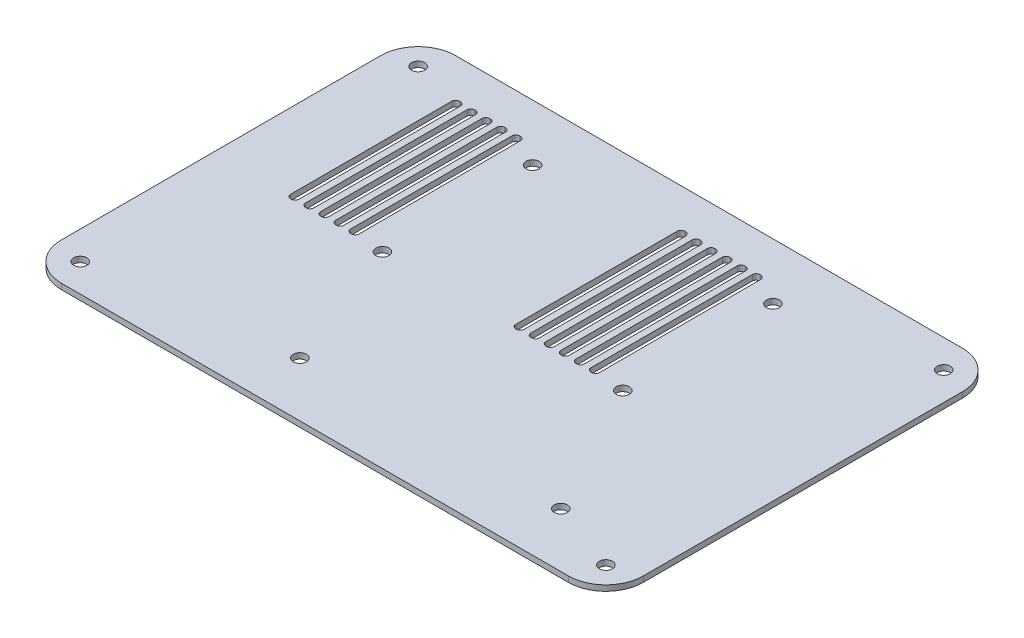
SolidWorks part; units mm, degrees
ref_plane "Front Plane" through (0, 0, 0) normal (0, 0, 1) x (1, 0, 0)
ref_plane "Top Plane" through (0, 0, 0) normal (0, 1, 0) x (1, 0, 0)
ref_plane "Right Plane" through (0, 0, 0) normal (1, 0, 0) x (0, 0, -1)
sketch "Sketch1" plane through (0, 0, 0) normal (0, 1, 0) x (1, 0, 0)
  line L1 (155, 105) -> (-155, 105)
  line L2 (155, 105) -> (155, -105)
  line L3 (155, -105) -> (-155, -105)
  line L4 (-155, 105) -> (-155, -105)
  line L5 (155, 105) -> (-155, -105) construction
  line L6 (155, -105) -> (-155, 105) construction
  circle A0 centre (-140, 90) radius 3.5
  circle A1 centre (140, 90) radius 3.5
  circle A2 centre (140, -90) radius 3.5
  circle A3 centre (-140, -90) radius 3.5
  circle A4 centre (102, -76) radius 3.5
  circle A5 centre (-37, -76) radius 3.5
  circle A6 centre (-64, 75) radius 3.5
  circle A7 centre (64, 75) radius 3.5
  circle A8 centre (-64, -5) radius 3.5
  circle A9 centre (64, -5) radius 3.5
  point P0 (0, 0)
  dimension "D3" = 15
  dimension "D4" = 7
  dimension "D5" = 15
  dimension "D6" = 15
  dimension "D7" = 15
  dimension "D8" = 15
  dimension "D9" = 15
  dimension "D10" = 15
  dimension "D11" = 15
  dimension "D12" = 53
  dimension "D13" = 29
  dimension "D14" = 29
  dimension "D15" = 139
  dimension "D16" = 30
  dimension "D17" = 91
  dimension "D18" = 91
  dimension "D19" = 80
  dimension "D20" = 80
  dimension "D1" = 310
  dimension "D2" = 210
extrude "Boss-Extrude1" add sketch "Sketch1" along normal blind 3
fillet "Fillet1" radius 20 4 edges at (155, 1.5, 105) (155, 1.5, -105) (-155, 1.5, -105) (-155, 1.5, 105)
sketch "Sketch2" plane through (0, 3, 0) normal (0, 1, 0) x (1, 0, 0)
  line L0 (-107, 83) -> (-107, -3)
  line L1 (-113, 85) -> (-112.5, 85)
  line L2 (-115, 83) -> (-115, -3)
  line L3 (-113, -5) -> (-112.5, -5)
  line L4 (-110.5, 83) -> (-110.5, -3)
  line L5 (-155, 85) -> (-155, -85) construction
  line L6 (135, 105) -> (-135, 105) construction
  line L7 (-105, 85) -> (-104.5, 85)
  line L8 (-102.5, 83) -> (-102.5, -3)
  line L9 (-105, -5) -> (-104.5, -5)
  line L10 (-99, 83) -> (-99, -3)
  line L11 (-97, 85) -> (-96.5, 85)
  line L12 (-94.5, 83) -> (-94.5, -3)
  line L13 (-97, -5) -> (-96.5, -5)
  line L14 (-91, 83) -> (-91, -3)
  line L15 (-89, 85) -> (-88.5, 85)
  line L16 (-86.5, 83) -> (-86.5, -3)
  line L17 (-89, -5) -> (-88.5, -5)
  line L18 (-83, 83) -> (-83, -3)
  line L19 (-81, 85) -> (-80.5, 85)
  line L20 (-78.5, 83) -> (-78.5, -3)
  line L21 (-81, -5) -> (-80.5, -5)
  line L62 (5, 83) -> (5, -3)
  line L63 (7, 85) -> (7.5, 85)
  line L64 (9.5, 83) -> (9.5, -3)
  line L65 (7, -5) -> (7.5, -5)
  line L66 (13, 83) -> (13, -3)
  line L67 (15, 85) -> (15.5, 85)
  line L68 (17.5, 83) -> (17.5, -3)
  line L69 (15, -5) -> (15.5, -5)
  line L70 (21, 83) -> (21, -3)
  line L71 (23, 85) -> (23.5, 85)
  line L72 (25.5, 83) -> (25.5, -3)
  line L73 (23, -5) -> (23.5, -5)
  line L74 (29, 83) -> (29, -3)
  line L75 (31, 85) -> (31.5, 85)
  line L76 (33.5, 83) -> (33.5, -3)
  line L77 (31, -5) -> (31.5, -5)
  line L78 (37, 83) -> (37, -3)
  line L79 (39, 85) -> (39.5, 85)
  line L80 (41.5, 83) -> (41.5, -3)
  line L81 (39, -5) -> (39.5, -5)
  line L82 (45, 83) -> (45, -3)
  line L83 (47, 85) -> (47.5, 85)
  line L84 (49.5, 83) -> (49.5, -3)
  line L85 (47, -5) -> (47.5, -5)
  arc A0 (-113, -5) -> (-115, -3) centre (-113, -3) cw
  arc A1 (-112.5, -5) -> (-110.5, -3) centre (-112.5, -3) ccw
  arc A2 (-110.5, 83) -> (-112.5, 85) centre (-112.5, 83) ccw
  arc A3 (-113, 85) -> (-115, 83) centre (-113, 83) ccw
  arc A4 (-105, 85) -> (-107, 83) centre (-105, 83) ccw
  arc A5 (-105, -5) -> (-107, -3) centre (-105, -3) cw
  arc A6 (-102.5, 83) -> (-104.5, 85) centre (-104.5, 83) ccw
  arc A7 (-104.5, -5) -> (-102.5, -3) centre (-104.5, -3) ccw
  arc A8 (-97, 85) -> (-99, 83) centre (-97, 83) ccw
  arc A9 (-97, -5) -> (-99, -3) centre (-97, -3) cw
  arc A10 (-94.5, 83) -> (-96.5, 85) centre (-96.5, 83) ccw
  arc A11 (-96.5, -5) -> (-94.5, -3) centre (-96.5, -3) ccw
  arc A12 (-89, 85) -> (-91, 83) centre (-89, 83) ccw
  arc A13 (-89, -5) -> (-91, -3) centre (-89, -3) cw
  arc A14 (-86.5, 83) -> (-88.5, 85) centre (-88.5, 83) ccw
  arc A15 (-88.5, -5) -> (-86.5, -3) centre (-88.5, -3) ccw
  arc A16 (-81, 85) -> (-83, 83) centre (-81, 83) ccw
  arc A17 (-81, -5) -> (-83, -3) centre (-81, -3) cw
  arc A18 (-78.5, 83) -> (-80.5, 85) centre (-80.5, 83) ccw
  arc A19 (-80.5, -5) -> (-78.5, -3) centre (-80.5, -3) ccw
  arc A60 (7, 85) -> (5, 83) centre (7, 83) ccw
  arc A61 (7, -5) -> (5, -3) centre (7, -3) cw
  arc A62 (9.5, 83) -> (7.5, 85) centre (7.5, 83) ccw
  arc A63 (7.5, -5) -> (9.5, -3) centre (7.5, -3) ccw
  arc A64 (15, 85) -> (13, 83) centre (15, 83) ccw
  arc A65 (15, -5) -> (13, -3) centre (15, -3) cw
  arc A66 (17.5, 83) -> (15.5, 85) centre (15.5, 83) ccw
  arc A67 (15.5, -5) -> (17.5, -3) centre (15.5, -3) ccw
  arc A68 (23, 85) -> (21, 83) centre (23, 83) ccw
  arc A69 (23, -5) -> (21, -3) centre (23, -3) cw
  arc A70 (25.5, 83) -> (23.5, 85) centre (23.5, 83) ccw
  arc A71 (23.5, -5) -> (25.5, -3) centre (23.5, -3) ccw
  arc A72 (31, 85) -> (29, 83) centre (31, 83) ccw
  arc A73 (31, -5) -> (29, -3) centre (31, -3) cw
  arc A74 (33.5, 83) -> (31.5, 85) centre (31.5, 83) ccw
  arc A75 (31.5, -5) -> (33.5, -3) centre (31.5, -3) ccw
  arc A76 (39, 85) -> (37, 83) centre (39, 83) ccw
  arc A77 (39, -5) -> (37, -3) centre (39, -3) cw
  arc A78 (41.5, 83) -> (39.5, 85) centre (39.5, 83) ccw
  arc A79 (39.5, -5) -> (41.5, -3) centre (39.5, -3) ccw
  arc A80 (47, 85) -> (45, 83) centre (47, 83) ccw
  arc A81 (47, -5) -> (45, -3) centre (47, -3) cw
  arc A82 (49.5, 83) -> (47.5, 85) centre (47.5, 83) ccw
  arc A83 (47.5, -5) -> (49.5, -3) centre (47.5, -3) ccw
  point P12 (-110.5, -5)
  point P15 (-110.5, 85)
  dimension "D5" = 2
  dimension "D1" = 40
  dimension "D2" = 20
  dimension "D3" = 4.5
  dimension "D4" = 90
extrude "Cut-Extrude2" cut sketch "Sketch2" against normal blind 10
